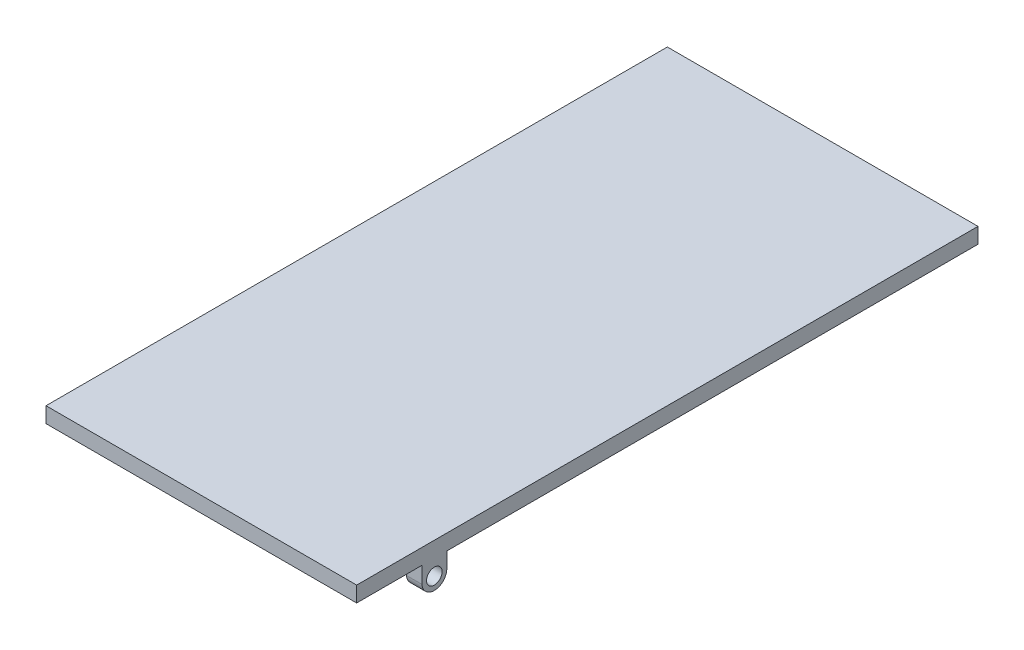
SolidWorks part; units mm, degrees
ref_plane "Front Plane" through (0, 0, 0) normal (0, 0, 1) x (1, 0, 0)
ref_plane "Top Plane" through (0, 0, 0) normal (0, 1, 0) x (1, 0, 0)
ref_plane "Right Plane" through (0, 0, 0) normal (1, 0, 0) x (0, 0, -1)
sketch "Sketch3" plane through (0, 0, 0) normal (0, 0, 1) x (1, 0, 0)
  line L1 (0, 0) -> (200, 0)
  line L2 (0, 0) -> (0, 10)
  line L3 (0, 10) -> (200, 10)
  line L4 (200, 0) -> (200, 10)
  dimension "D1" = 10
  dimension "D2" = 200
extrude "Boss-Extrude1" add sketch "Sketch3" along normal blind 400
sketch "Sketch4" plane through (200, 0, 0) normal (1, 0, 0) x (0, 0, -1)
  line L0 (-350, 47.3528) -> (-350, -38.109) construction
  line L1 (-400, 0) -> (-400, 10) construction
  line L2 (-400, 0) -> (0, 0) construction
  line L3 (-358, 0) -> (-342, 0)
  line L4 (-358, 0) -> (-358, -20)
  line L6 (-342, 0) -> (-342, -10.5969)
  circle A0 centre (-350, -10) radius 5
  arc A1 (-358, -9.4031) -> (-342, -9.4031) centre (-350, -10) ccw
  point P4 (-400, 5)
  line M9 (-400, 0) -> (0, 0)
  dimension "D5" = 10
  dimension "D1" = 50
  dimension "D2" = 8
  dimension "D3" = 8
extrude "Boss-Extrude2" add sketch "Sketch4" against normal blind 200 contours L0 L4 A1 A0 M9 | L3 L0 A0 A1 L6
sketch "Sketch5" plane through (0, 0, 0) normal (0, -1, 0) x (1, 0, 0)
  line L0 (0, 358) -> (200, 358) construction
  line L1 (10, 358) -> (190, 358)
  line L2 (10, 358) -> (10, 342)
  line L3 (10, 342) -> (190, 342)
  line L4 (190, 358) -> (190, 342)
  line L5 (0, 342) -> (200, 342) construction
  line L6 (0, 358) -> (0, 342) construction
  line L7 (200, 342) -> (200, 358) construction
  point P12 (200, 350)
  dimension "D1" = 10
  dimension "D2" = 10
extrude "Cut-Extrude1" cut sketch "Sketch5" along normal blind 75
